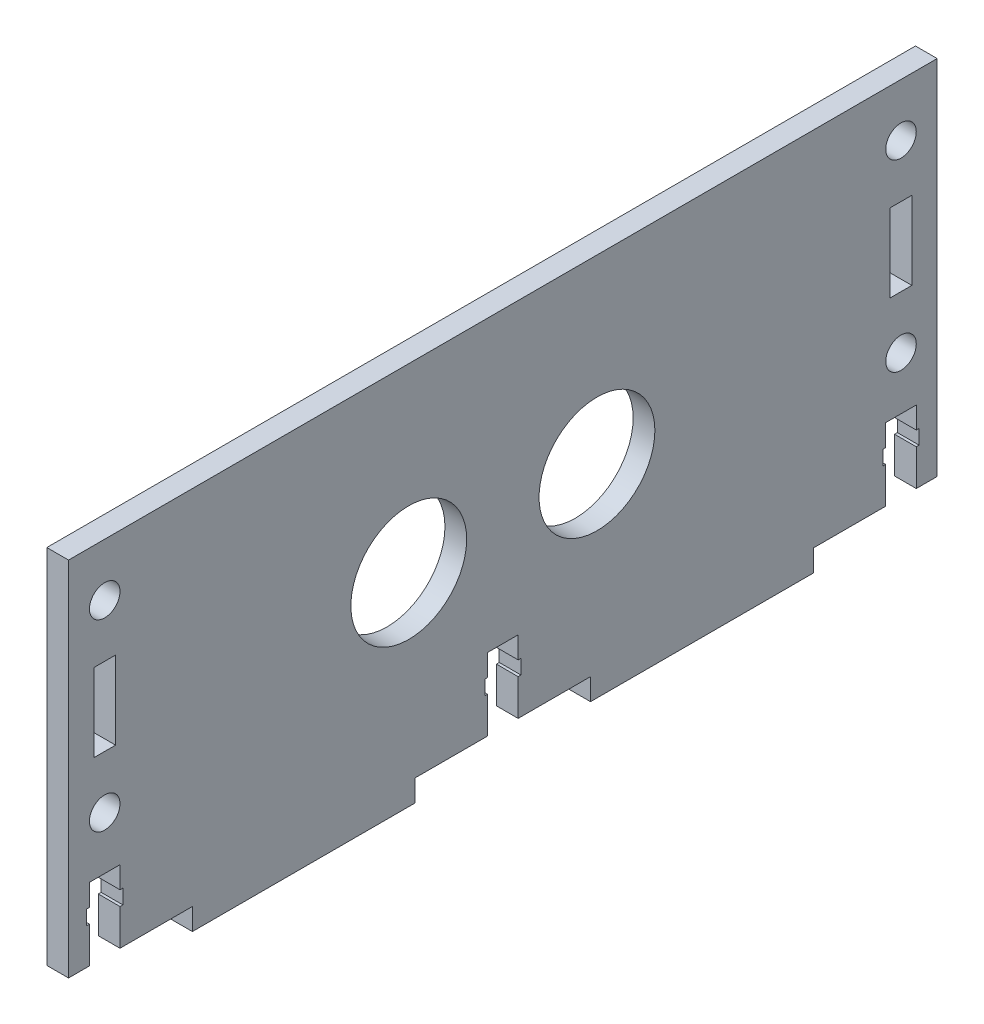
SolidWorks part; units mm, degrees
ref_plane "Front Plane" through (0, 0, 0) normal (0, 0, 1) x (1, 0, 0)
ref_plane "Top Plane" through (0, 0, 0) normal (0, 1, 0) x (1, 0, 0)
ref_plane "Right Plane" through (0, 0, 0) normal (1, 0, 0) x (0, 0, -1)
sketch "Sketch2" plane through (0, 0, 0) normal (1, 0, 0) x (0, 0, -1)
  line L0 (0, 0) -> (2.89, 0)
  line L1 (0, 0) -> (0, 50)
  line L2 (0, 50) -> (120, 50)
  line L3 (120, 50) -> (120, 0)
  line L4 (112.5, 5) -> (112.5, 7)
  line L5 (47.89, -3) -> (47.89, 0)
  line L7 (7.11, 0) -> (7.11, 5)
  line L8 (7.11, 5) -> (7.5, 5)
  line L9 (7.5, 5) -> (7.5, 7)
  line L10 (7.5, 7) -> (7.11, 7)
  line L11 (7.11, 7) -> (7.11, 10)
  line L13 (7.11, 10) -> (2.89, 10)
  line L14 (2.89, 10) -> (2.89, 7)
  line L15 (2.89, 7) -> (2.5, 7)
  line L16 (2.5, 7) -> (2.5, 5)
  line L17 (2.5, 5) -> (2.89, 5)
  line L18 (2.89, 5) -> (2.89, 0)
  line L19 (117.11, 5) -> (117.11, 0)
  line L20 (117.5, 5) -> (117.11, 5)
  line L21 (117.5, 7) -> (117.5, 5)
  line L22 (117.11, 7) -> (117.5, 7)
  line L23 (117.11, 10) -> (117.11, 7)
  line L24 (112.89, 10) -> (117.11, 10)
  line L25 (112.89, 7) -> (112.89, 10)
  line L26 (112.5, 7) -> (112.89, 7)
  line L27 (112.89, 5) -> (112.5, 5)
  line L28 (112.89, 0) -> (112.89, 5)
  line L30 (47.89, 0) -> (57.89, 0)
  line L31 (17.11, -3) -> (17.11, 0)
  line L32 (17.11, -3) -> (47.89, -3)
  line L33 (62.11, 10) -> (57.89, 10)
  line L34 (7.11, 0) -> (17.11, 0)
  line L35 (62.11, 0) -> (62.11, 5)
  line L36 (62.11, 5) -> (62.5, 5)
  line L37 (62.5, 7) -> (62.11, 7)
  line L38 (62.11, 7) -> (62.11, 10)
  line L39 (57.89, 10) -> (57.89, 7)
  line L40 (57.89, 7) -> (57.5, 7)
  line L41 (57.5, 7) -> (57.5, 5)
  line L42 (57.5, 5) -> (57.89, 5)
  line L43 (57.89, 5) -> (57.89, 0)
  line L44 (62.5, 5) -> (62.5, 7)
  line L45 (102.89, -3) -> (102.89, 0)
  line L46 (72.11, -3) -> (72.11, 0)
  line L47 (102.89, -3) -> (72.11, -3)
  line L48 (102.89, 0) -> (112.89, 0)
  line L49 (62.11, 0) -> (72.11, 0)
  line L50 (117.11, 0) -> (120, 0)
  line L51 (116.5, 24.61) -> (113.5, 24.61)
  line L52 (3.5, 35.39) -> (6.5, 35.39)
  line L53 (3.5, 35.39) -> (3.5, 24.61)
  line L54 (113.5, 35.39) -> (113.5, 24.61)
  line L55 (3.5, 24.61) -> (6.5, 24.61)
  line L56 (6.5, 35.39) -> (6.5, 24.61)
  line L57 (116.5, 35.39) -> (113.5, 35.39)
  line L58 (116.5, 35.39) -> (116.5, 24.61)
extrude "Boss-Extrude2" add sketch "Sketch2" along normal blind 3
sketch "Sketch7" plane through (3, 0, 0) normal (1, 0, 0) x (0, 0, -1)
  line L0 (5, 24.61) -> (5, 10)
  line L1 (6.5, 35.39) -> (3.5, 35.39) construction
  line L2 (5, 35.39) -> (5, 50)
  line L3 (120, 50) -> (0, 50) construction
  line L4 (3.5, 24.61) -> (6.5, 24.61) construction
  line L5 (2.89, 10) -> (7.11, 10) construction
  line L8 (115, 35.39) -> (115, 50)
  line L9 (115, 24.61) -> (115, 10)
hole_wizard "Hole for M3 300® SC Nuts (SP)1" positions "Sketch8" profile "Sketch9" hole size "M3x0.5" standard "PEM® Metric" end condition through all
sketch "Sketch8" plane through (3, 0, 0) normal (1, 0, 0) x (0, 0, -1)
  line L0 (5, 35.39) -> (5, 50) construction
  line L1 (5, 24.61) -> (5, 10) construction
  line L2 (115, 35.39) -> (115, 50) construction
  line L3 (115, 24.61) -> (115, 10) construction
  point P0 (5, 42.695)
  point P4 (5, 17.305)
  point P8 (115, 42.695)
  point P12 (115, 17.305)
sketch "Sketch9" plane through (3, 42.695, -5) normal (0, 1, 0) x (0, 0, -1)
  line L0 (0, 0) -> (0, 3)
  line L1 (0, 3) -> (2.11, 3)
  line L2 (2.11, 3) -> (2.11, 0)
  line L5 (2.11, 0) -> (0, 0)
  line L11 (0, -6.35) -> (0, 107.95) construction
  dimension "Thru Hole Dia." = 4.22
  dimension "Thru Hole Depth" = 3
sketch "Sketch10" plane through (3, 0, 0) normal (1, 0, 0) x (0, 0, -1)
  line L7 (37.5, 35) -> (82.5, 35)
  line L8 (37.5, 35) -> (37.5, 15)
  line L9 (37.5, 15) -> (82.5, 15)
  line L10 (82.5, 35) -> (82.5, 15)
  circle A0 centre (73, 25) radius 8
  circle A1 centre (47, 25) radius 8
extrude "Cut-Extrude1" cut sketch "Sketch10" against normal blind 10 contours A0 | A1
